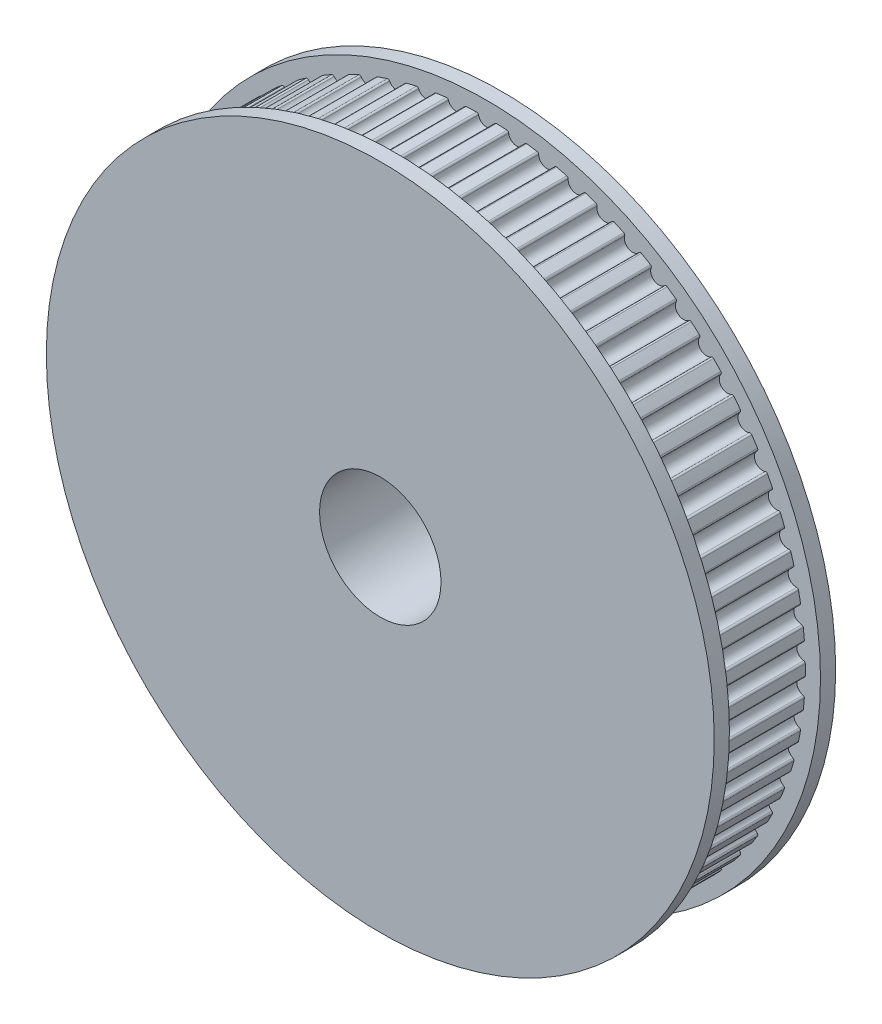
SolidWorks part; units mm, degrees
material "Plain Carbon Steel"
ref_plane "Front Plane" through (0, 0, 0) normal (0, 0, 1) x (1, 0, 0)
ref_plane "Top Plane" through (0, 0, 0) normal (0, 1, 0) x (1, 0, 0)
ref_plane "Right Plane" through (0, 0, 0) normal (1, 0, 0) x (0, 0, -1)
sketch "Sketch1" plane through (0, 0, 0) normal (0, 0, 1) x (1, 0, 0)
  circle A0 centre (0, 0) radius 4
  arc A1 (-0.655, 20.9898) -> (0.655, 20.9898) centre (0, 0) ccw
  arc A2 (-0.5287, 20.8902) -> (0.5287, 20.8902) centre (0, 21) ccw
  arc A3 (0.5287, 20.8902) -> (0.655, 20.9898) centre (0.6511, 20.8648) cw
  arc A4 (-0.5287, 20.8902) -> (-0.655, 20.9898) centre (-0.6511, 20.8648) ccw
  arc A5 (1.3432, 20.957) -> (2.6473, 20.8325) centre (0, 0) ccw
  arc A6 (1.4594, 20.8459) -> (1.3432, 20.957) centre (1.3352, 20.8323) ccw
  arc A7 (1.4594, 20.8459) -> (2.5121, 20.7454) centre (1.9962, 20.9049) ccw
  arc A8 (2.5121, 20.7454) -> (2.6473, 20.8325) centre (2.6315, 20.7085) cw
  arc A9 (3.3292, 20.7344) -> (4.6155, 20.4865) centre (0, 0) ccw
  arc A10 (3.4343, 20.6128) -> (3.3292, 20.7344) centre (3.3093, 20.611) ccw
  arc A11 (3.4343, 20.6128) -> (4.4727, 20.4127) centre (3.9743, 20.6205) ccw
  arc A12 (4.4727, 20.4127) -> (4.6155, 20.4865) centre (4.5881, 20.3646) cw
  arc A13 (5.285, 20.3241) -> (6.542, 19.955) centre (0, 0) ccw
  arc A14 (5.3782, 20.193) -> (5.285, 20.3241) centre (5.2536, 20.2031) ccw
  arc A15 (5.3782, 20.193) -> (6.3928, 19.8951) centre (5.9164, 20.1494) ccw
  arc A16 (6.3928, 19.8951) -> (6.542, 19.955) centre (6.5031, 19.8362) cw
  arc A17 (7.193, 19.7297) -> (8.4092, 19.2428) centre (0, 0) ccw
  arc A18 (7.2733, 19.5903) -> (7.193, 19.7297) centre (7.1502, 19.6122) ccw
  arc A19 (7.2733, 19.5903) -> (8.255, 19.1973) centre (7.8049, 19.4957) ccw
  arc A20 (8.255, 19.1973) -> (8.4092, 19.2428) centre (8.3592, 19.1283) cw
  arc A21 (9.0359, 18.9566) -> (10.2003, 18.3563) centre (0, 0) ccw
  arc A22 (9.1025, 18.8103) -> (9.0359, 18.9566) centre (8.9821, 18.8438) ccw
  arc A23 (9.1025, 18.8103) -> (10.0424, 18.3257) centre (9.6228, 18.6655) ccw
  arc A24 (10.0424, 18.3257) -> (10.2003, 18.3563) centre (10.1396, 18.2471) cw
  arc A25 (10.7969, 18.0119) -> (11.899, 17.3036) centre (0, 0) ccw
  arc A26 (10.8493, 17.8598) -> (10.7969, 18.0119) centre (10.7326, 17.9046) ccw
  arc A27 (10.8493, 17.8598) -> (11.7389, 17.2881) centre (11.3535, 17.6663) ccw
  arc A28 (11.7389, 17.2881) -> (11.899, 17.3036) centre (11.8281, 17.2006) cw
  arc A29 (12.4601, 16.904) -> (13.4899, 16.0942) centre (0, 0) ccw
  arc A30 (12.4979, 16.7477) -> (12.4601, 16.904) centre (12.386, 16.8034) ccw
  arc A31 (12.4979, 16.7477) -> (13.3291, 16.094) centre (12.9813, 16.5071) ccw
  arc A32 (13.3291, 16.094) -> (13.4899, 16.0942) centre (13.4096, 15.9984) cw
  arc A33 (14.0105, 15.643) -> (14.9587, 14.739) centre (0, 0) ccw
  arc A34 (14.0333, 15.4838) -> (14.0105, 15.643) centre (13.9272, 15.5499) ccw
  arc A35 (14.0333, 15.4838) -> (14.7986, 14.7541) centre (14.4917, 15.1984) ccw
  arc A36 (14.7986, 14.7541) -> (14.9587, 14.739) centre (14.8696, 14.6513) cw
  arc A37 (15.4341, 14.2404) -> (16.292, 13.2504) centre (0, 0) ccw
  arc A38 (15.4416, 14.0798) -> (15.4341, 14.2404) centre (15.3422, 14.1557) ccw
  arc A39 (15.4416, 14.0798) -> (16.134, 13.2806) centre (15.8707, 13.7521) ccw
  arc A40 (16.134, 13.2806) -> (16.292, 13.2504) centre (16.195, 13.1715) cw
  arc A41 (16.7178, 12.7088) -> (17.4777, 11.6417) centre (0, 0) ccw
  arc A42 (16.71, 12.5482) -> (16.7178, 12.7088) centre (16.6183, 12.6332) ccw
  arc A43 (16.71, 12.5482) -> (17.3234, 11.6868) centre (17.1061, 12.1812) ccw
  arc A44 (17.3234, 11.6868) -> (17.4777, 11.6417) centre (17.3737, 11.5724) cw
  arc A45 (17.8502, 11.0622) -> (18.5052, 9.9276) centre (0, 0) ccw
  arc A46 (17.8271, 10.903) -> (17.8502, 11.0622) centre (17.7439, 10.9963) ccw
  arc A47 (17.8271, 10.903) -> (18.3559, 9.9872) centre (18.1865, 10.5) ccw
  arc A48 (18.3559, 9.9872) -> (18.5052, 9.9276) centre (18.395, 9.8685) cw
  arc A49 (18.8209, 9.3153) -> (19.3651, 8.1236) centre (0, 0) ccw
  arc A50 (18.7828, 9.1591) -> (18.8209, 9.3153) centre (18.7088, 9.2598) ccw
  arc A51 (18.7828, 9.1591) -> (19.2221, 8.1972) centre (19.1023, 8.7237) ccw
  arc A52 (19.2221, 8.1972) -> (19.3651, 8.1236) centre (19.2498, 8.0753) cw
  arc A53 (19.6211, 7.4841) -> (20.0496, 6.2461) centre (0, 0) ccw
  arc A54 (19.5684, 7.3322) -> (19.6211, 7.4841) centre (19.5043, 7.4395) ccw
  arc A55 (19.5684, 7.3322) -> (19.9142, 6.3329) centre (19.845, 6.8684) ccw
  arc A56 (19.9142, 6.3329) -> (20.0496, 6.2461) centre (19.9303, 6.2089) cw
  arc A57 (20.2437, 5.5851) -> (20.5525, 4.312) centre (0, 0) ccw
  arc A58 (20.1767, 5.4389) -> (20.2437, 5.5851) centre (20.1232, 5.5518) ccw
  arc A59 (20.1767, 5.4389) -> (20.426, 4.4112) centre (20.408, 4.9509) ccw
  arc A60 (20.426, 4.4112) -> (20.5525, 4.312) centre (20.4302, 4.2863) cw
  arc A61 (20.6829, 3.6355) -> (20.8694, 2.3388) centre (0, 0) ccw
  arc A62 (20.6024, 3.4963) -> (20.6829, 3.6355) centre (20.5598, 3.6139) ccw
  arc A63 (20.6024, 3.4963) -> (20.7529, 2.4496) centre (20.7863, 2.9886) ccw
  arc A64 (20.7529, 2.4496) -> (20.8694, 2.3388) centre (20.7451, 2.3249) cw
  arc A65 (20.9348, 1.653) -> (20.9972, 0.3445) centre (0, 0) ccw
  arc A66 (20.8414, 1.5221) -> (20.9348, 1.653) centre (20.8102, 1.6432) ccw
  arc A67 (20.8414, 1.5221) -> (20.8917, 0.4659) centre (20.9762, 0.9992) ccw
  arc A68 (20.8917, 0.4659) -> (20.9972, 0.3445) centre (20.8722, 0.3424) cw
  arc A69 (20.9972, -0.3445) -> (20.9348, -1.653) centre (0, 0) ccw
  arc A70 (20.8917, -0.4659) -> (20.9972, -0.3445) centre (20.8722, -0.3424) ccw
  arc A71 (20.8917, -0.4659) -> (20.8414, -1.5221) centre (20.9762, -0.9992) ccw
  arc A72 (20.8414, -1.5221) -> (20.9348, -1.653) centre (20.8102, -1.6432) cw
  arc A73 (20.8694, -2.3388) -> (20.6829, -3.6355) centre (0, 0) ccw
  arc A74 (20.7529, -2.4496) -> (20.8694, -2.3388) centre (20.7451, -2.3249) ccw
  arc A75 (20.7529, -2.4496) -> (20.6024, -3.4963) centre (20.7863, -2.9886) ccw
  arc A76 (20.6024, -3.4963) -> (20.6829, -3.6355) centre (20.5598, -3.6139) cw
  arc A77 (20.5525, -4.312) -> (20.2437, -5.5851) centre (0, 0) ccw
  arc A78 (20.426, -4.4112) -> (20.5525, -4.312) centre (20.4302, -4.2863) ccw
  arc A79 (20.426, -4.4112) -> (20.1767, -5.4389) centre (20.408, -4.9509) ccw
  arc A80 (20.1767, -5.4389) -> (20.2437, -5.5851) centre (20.1232, -5.5518) cw
  arc A81 (20.0496, -6.2461) -> (19.6211, -7.4841) centre (0, 0) ccw
  arc A82 (19.9142, -6.3329) -> (20.0496, -6.2461) centre (19.9303, -6.2089) ccw
  arc A83 (19.9142, -6.3329) -> (19.5684, -7.3322) centre (19.845, -6.8684) ccw
  arc A84 (19.5684, -7.3322) -> (19.6211, -7.4841) centre (19.5043, -7.4395) cw
  arc A85 (19.3651, -8.1236) -> (18.8209, -9.3153) centre (0, 0) ccw
  arc A86 (19.2221, -8.1972) -> (19.3651, -8.1236) centre (19.2498, -8.0753) ccw
  arc A87 (19.2221, -8.1972) -> (18.7828, -9.1591) centre (19.1023, -8.7237) ccw
  arc A88 (18.7828, -9.1591) -> (18.8209, -9.3153) centre (18.7088, -9.2598) cw
  arc A89 (18.5052, -9.9276) -> (17.8502, -11.0622) centre (0, 0) ccw
  arc A90 (18.3559, -9.9872) -> (18.5052, -9.9276) centre (18.395, -9.8685) ccw
  arc A91 (18.3559, -9.9872) -> (17.8271, -10.903) centre (18.1865, -10.5) ccw
  arc A92 (17.8271, -10.903) -> (17.8502, -11.0622) centre (17.7439, -10.9963) cw
  arc A93 (17.4777, -11.6417) -> (16.7178, -12.7088) centre (0, 0) ccw
  arc A94 (17.3234, -11.6868) -> (17.4777, -11.6417) centre (17.3737, -11.5724) ccw
  arc A95 (17.3234, -11.6868) -> (16.71, -12.5482) centre (17.1061, -12.1812) ccw
  arc A96 (16.71, -12.5482) -> (16.7178, -12.7088) centre (16.6183, -12.6332) cw
  arc A97 (16.292, -13.2504) -> (15.4341, -14.2404) centre (0, 0) ccw
  arc A98 (16.134, -13.2806) -> (16.292, -13.2504) centre (16.195, -13.1715) ccw
  arc A99 (16.134, -13.2806) -> (15.4416, -14.0798) centre (15.8707, -13.7521) ccw
  arc A100 (15.4416, -14.0798) -> (15.4341, -14.2404) centre (15.3422, -14.1557) cw
  arc A101 (14.9587, -14.739) -> (14.0105, -15.643) centre (0, 0) ccw
  arc A102 (14.7986, -14.7541) -> (14.9587, -14.739) centre (14.8696, -14.6513) ccw
  arc A103 (14.7986, -14.7541) -> (14.0333, -15.4838) centre (14.4917, -15.1984) ccw
  arc A104 (14.0333, -15.4838) -> (14.0105, -15.643) centre (13.9272, -15.5499) cw
  arc A105 (13.4899, -16.0942) -> (12.4601, -16.904) centre (0, 0) ccw
  arc A106 (13.3291, -16.094) -> (13.4899, -16.0942) centre (13.4096, -15.9984) ccw
  arc A107 (13.3291, -16.094) -> (12.4979, -16.7477) centre (12.9813, -16.5071) ccw
  arc A108 (12.4979, -16.7477) -> (12.4601, -16.904) centre (12.386, -16.8034) cw
  arc A109 (11.899, -17.3036) -> (10.7969, -18.0119) centre (0, 0) ccw
  arc A110 (11.7389, -17.2881) -> (11.899, -17.3036) centre (11.8281, -17.2006) ccw
  arc A111 (11.7389, -17.2881) -> (10.8493, -17.8598) centre (11.3535, -17.6663) ccw
  arc A112 (10.8493, -17.8598) -> (10.7969, -18.0119) centre (10.7326, -17.9046) cw
  arc A113 (10.2003, -18.3563) -> (9.0359, -18.9566) centre (0, 0) ccw
  arc A114 (10.0424, -18.3257) -> (10.2003, -18.3563) centre (10.1396, -18.2471) ccw
  arc A115 (10.0424, -18.3257) -> (9.1025, -18.8103) centre (9.6228, -18.6655) ccw
  arc A116 (9.1025, -18.8103) -> (9.0359, -18.9566) centre (8.9821, -18.8438) cw
  arc A117 (8.4092, -19.2428) -> (7.193, -19.7297) centre (0, 0) ccw
  arc A118 (8.255, -19.1973) -> (8.4092, -19.2428) centre (8.3592, -19.1283) ccw
  arc A119 (8.255, -19.1973) -> (7.2733, -19.5903) centre (7.8049, -19.4957) ccw
  arc A120 (7.2733, -19.5903) -> (7.193, -19.7297) centre (7.1502, -19.6122) cw
  arc A121 (6.542, -19.955) -> (5.285, -20.3241) centre (0, 0) ccw
  arc A122 (6.3928, -19.8951) -> (6.542, -19.955) centre (6.5031, -19.8362) ccw
  arc A123 (6.3928, -19.8951) -> (5.3782, -20.193) centre (5.9164, -20.1494) ccw
  arc A124 (5.3782, -20.193) -> (5.285, -20.3241) centre (5.2536, -20.2031) cw
  arc A125 (4.6155, -20.4865) -> (3.3292, -20.7344) centre (0, 0) ccw
  arc A126 (4.4727, -20.4127) -> (4.6155, -20.4865) centre (4.5881, -20.3646) ccw
  arc A127 (4.4727, -20.4127) -> (3.4343, -20.6128) centre (3.9743, -20.6205) ccw
  arc A128 (3.4343, -20.6128) -> (3.3292, -20.7344) centre (3.3093, -20.611) cw
  arc A129 (2.6473, -20.8325) -> (1.3432, -20.957) centre (0, 0) ccw
  arc A130 (2.5121, -20.7454) -> (2.6473, -20.8325) centre (2.6315, -20.7085) ccw
  arc A131 (2.5121, -20.7454) -> (1.4594, -20.8459) centre (1.9962, -20.9049) ccw
  arc A132 (1.4594, -20.8459) -> (1.3432, -20.957) centre (1.3352, -20.8323) cw
  arc A133 (0.655, -20.9898) -> (-0.655, -20.9898) centre (0, 0) ccw
  arc A134 (0.5287, -20.8902) -> (0.655, -20.9898) centre (0.6511, -20.8648) ccw
  arc A135 (0.5287, -20.8902) -> (-0.5287, -20.8902) centre (0, -21) ccw
  arc A136 (-0.5287, -20.8902) -> (-0.655, -20.9898) centre (-0.6511, -20.8648) cw
  arc A137 (-1.3432, -20.957) -> (-2.6473, -20.8325) centre (0, 0) ccw
  arc A138 (-1.4594, -20.8459) -> (-1.3432, -20.957) centre (-1.3352, -20.8323) ccw
  arc A139 (-1.4594, -20.8459) -> (-2.5121, -20.7454) centre (-1.9962, -20.9049) ccw
  arc A140 (-2.5121, -20.7454) -> (-2.6473, -20.8325) centre (-2.6315, -20.7085) cw
  arc A141 (-3.3292, -20.7344) -> (-4.6155, -20.4865) centre (0, 0) ccw
  arc A142 (-3.4343, -20.6128) -> (-3.3292, -20.7344) centre (-3.3093, -20.611) ccw
  arc A143 (-3.4343, -20.6128) -> (-4.4727, -20.4127) centre (-3.9743, -20.6205) ccw
  arc A144 (-4.4727, -20.4127) -> (-4.6155, -20.4865) centre (-4.5881, -20.3646) cw
  arc A145 (-5.285, -20.3241) -> (-6.542, -19.955) centre (0, 0) ccw
  arc A146 (-5.3782, -20.193) -> (-5.285, -20.3241) centre (-5.2536, -20.2031) ccw
  arc A147 (-5.3782, -20.193) -> (-6.3928, -19.8951) centre (-5.9164, -20.1494) ccw
  arc A148 (-6.3928, -19.8951) -> (-6.542, -19.955) centre (-6.5031, -19.8362) cw
  arc A149 (-7.193, -19.7297) -> (-8.4092, -19.2428) centre (0, 0) ccw
  arc A150 (-7.2733, -19.5903) -> (-7.193, -19.7297) centre (-7.1502, -19.6122) ccw
  arc A151 (-7.2733, -19.5903) -> (-8.255, -19.1973) centre (-7.8049, -19.4957) ccw
  arc A152 (-8.255, -19.1973) -> (-8.4092, -19.2428) centre (-8.3592, -19.1283) cw
  arc A153 (-9.0359, -18.9566) -> (-10.2003, -18.3563) centre (0, 0) ccw
  arc A154 (-9.1025, -18.8103) -> (-9.0359, -18.9566) centre (-8.9821, -18.8438) ccw
  arc A155 (-9.1025, -18.8103) -> (-10.0424, -18.3257) centre (-9.6228, -18.6655) ccw
  arc A156 (-10.0424, -18.3257) -> (-10.2003, -18.3563) centre (-10.1396, -18.2471) cw
  arc A157 (-10.7969, -18.0119) -> (-11.899, -17.3036) centre (0, 0) ccw
  arc A158 (-10.8493, -17.8598) -> (-10.7969, -18.0119) centre (-10.7326, -17.9046) ccw
  arc A159 (-10.8493, -17.8598) -> (-11.7389, -17.2881) centre (-11.3535, -17.6663) ccw
  arc A160 (-11.7389, -17.2881) -> (-11.899, -17.3036) centre (-11.8281, -17.2006) cw
  arc A161 (-12.4601, -16.904) -> (-13.4899, -16.0942) centre (0, 0) ccw
  arc A162 (-12.4979, -16.7477) -> (-12.4601, -16.904) centre (-12.386, -16.8034) ccw
  arc A163 (-12.4979, -16.7477) -> (-13.3291, -16.094) centre (-12.9813, -16.5071) ccw
  arc A164 (-13.3291, -16.094) -> (-13.4899, -16.0942) centre (-13.4096, -15.9984) cw
  arc A165 (-14.0105, -15.643) -> (-14.9587, -14.739) centre (0, 0) ccw
  arc A166 (-14.0333, -15.4838) -> (-14.0105, -15.643) centre (-13.9272, -15.5499) ccw
  arc A167 (-14.0333, -15.4838) -> (-14.7986, -14.7541) centre (-14.4917, -15.1984) ccw
  arc A168 (-14.7986, -14.7541) -> (-14.9587, -14.739) centre (-14.8696, -14.6513) cw
  arc A169 (-15.4341, -14.2404) -> (-16.292, -13.2504) centre (0, 0) ccw
  arc A170 (-15.4416, -14.0798) -> (-15.4341, -14.2404) centre (-15.3422, -14.1557) ccw
  arc A171 (-15.4416, -14.0798) -> (-16.134, -13.2806) centre (-15.8707, -13.7521) ccw
  arc A172 (-16.134, -13.2806) -> (-16.292, -13.2504) centre (-16.195, -13.1715) cw
  arc A173 (-16.7178, -12.7088) -> (-17.4777, -11.6417) centre (0, 0) ccw
  arc A174 (-16.71, -12.5482) -> (-16.7178, -12.7088) centre (-16.6183, -12.6332) ccw
  arc A175 (-16.71, -12.5482) -> (-17.3234, -11.6868) centre (-17.1061, -12.1812) ccw
  arc A176 (-17.3234, -11.6868) -> (-17.4777, -11.6417) centre (-17.3737, -11.5724) cw
  arc A177 (-17.8502, -11.0622) -> (-18.5052, -9.9276) centre (0, 0) ccw
  arc A178 (-17.8271, -10.903) -> (-17.8502, -11.0622) centre (-17.7439, -10.9963) ccw
  arc A179 (-17.8271, -10.903) -> (-18.3559, -9.9872) centre (-18.1865, -10.5) ccw
  arc A180 (-18.3559, -9.9872) -> (-18.5052, -9.9276) centre (-18.395, -9.8685) cw
  arc A181 (-18.8209, -9.3153) -> (-19.3651, -8.1236) centre (0, 0) ccw
  arc A182 (-18.7828, -9.1591) -> (-18.8209, -9.3153) centre (-18.7088, -9.2598) ccw
  arc A183 (-18.7828, -9.1591) -> (-19.2221, -8.1972) centre (-19.1023, -8.7237) ccw
  arc A184 (-19.2221, -8.1972) -> (-19.3651, -8.1236) centre (-19.2498, -8.0753) cw
  arc A185 (-19.6211, -7.4841) -> (-20.0496, -6.2461) centre (0, 0) ccw
  arc A186 (-19.5684, -7.3322) -> (-19.6211, -7.4841) centre (-19.5043, -7.4395) ccw
  arc A187 (-19.5684, -7.3322) -> (-19.9142, -6.3329) centre (-19.845, -6.8684) ccw
  arc A188 (-19.9142, -6.3329) -> (-20.0496, -6.2461) centre (-19.9303, -6.2089) cw
  arc A189 (-20.2437, -5.5851) -> (-20.5525, -4.312) centre (0, 0) ccw
  arc A190 (-20.1767, -5.4389) -> (-20.2437, -5.5851) centre (-20.1232, -5.5518) ccw
  arc A191 (-20.1767, -5.4389) -> (-20.426, -4.4112) centre (-20.408, -4.9509) ccw
  arc A192 (-20.426, -4.4112) -> (-20.5525, -4.312) centre (-20.4302, -4.2863) cw
  arc A193 (-20.6829, -3.6355) -> (-20.8694, -2.3388) centre (0, 0) ccw
  arc A194 (-20.6024, -3.4963) -> (-20.6829, -3.6355) centre (-20.5598, -3.6139) ccw
  arc A195 (-20.6024, -3.4963) -> (-20.7529, -2.4496) centre (-20.7863, -2.9886) ccw
  arc A196 (-20.7529, -2.4496) -> (-20.8694, -2.3388) centre (-20.7451, -2.3249) cw
  arc A197 (-20.9348, -1.653) -> (-20.9972, -0.3445) centre (0, 0) ccw
  arc A198 (-20.8414, -1.5221) -> (-20.9348, -1.653) centre (-20.8102, -1.6432) ccw
  arc A199 (-20.8414, -1.5221) -> (-20.8917, -0.4659) centre (-20.9762, -0.9992) ccw
  arc A200 (-20.8917, -0.4659) -> (-20.9972, -0.3445) centre (-20.8722, -0.3424) cw
  arc A201 (-20.9972, 0.3445) -> (-20.9348, 1.653) centre (0, 0) ccw
  arc A202 (-20.8917, 0.4659) -> (-20.9972, 0.3445) centre (-20.8722, 0.3424) ccw
  arc A203 (-20.8917, 0.4659) -> (-20.8414, 1.5221) centre (-20.9762, 0.9992) ccw
  arc A204 (-20.8414, 1.5221) -> (-20.9348, 1.653) centre (-20.8102, 1.6432) cw
  arc A205 (-20.8694, 2.3388) -> (-20.6829, 3.6355) centre (0, 0) ccw
  arc A206 (-20.7529, 2.4496) -> (-20.8694, 2.3388) centre (-20.7451, 2.3249) ccw
  arc A207 (-20.7529, 2.4496) -> (-20.6024, 3.4963) centre (-20.7863, 2.9886) ccw
  arc A208 (-20.6024, 3.4963) -> (-20.6829, 3.6355) centre (-20.5598, 3.6139) cw
  arc A209 (-20.5525, 4.312) -> (-20.2437, 5.5851) centre (0, 0) ccw
  arc A210 (-20.426, 4.4112) -> (-20.5525, 4.312) centre (-20.4302, 4.2863) ccw
  arc A211 (-20.426, 4.4112) -> (-20.1767, 5.4389) centre (-20.408, 4.9509) ccw
  arc A212 (-20.1767, 5.4389) -> (-20.2437, 5.5851) centre (-20.1232, 5.5518) cw
  arc A213 (-20.0496, 6.2461) -> (-19.6211, 7.4841) centre (0, 0) ccw
  arc A214 (-19.9142, 6.3329) -> (-20.0496, 6.2461) centre (-19.9303, 6.2089) ccw
  arc A215 (-19.9142, 6.3329) -> (-19.5684, 7.3322) centre (-19.845, 6.8684) ccw
  arc A216 (-19.5684, 7.3322) -> (-19.6211, 7.4841) centre (-19.5043, 7.4395) cw
  arc A217 (-19.3651, 8.1236) -> (-18.8209, 9.3153) centre (0, 0) ccw
  arc A218 (-19.2221, 8.1972) -> (-19.3651, 8.1236) centre (-19.2498, 8.0753) ccw
  arc A219 (-19.2221, 8.1972) -> (-18.7828, 9.1591) centre (-19.1023, 8.7237) ccw
  arc A220 (-18.7828, 9.1591) -> (-18.8209, 9.3153) centre (-18.7088, 9.2598) cw
  arc A221 (-18.5052, 9.9276) -> (-17.8502, 11.0622) centre (0, 0) ccw
  arc A222 (-18.3559, 9.9872) -> (-18.5052, 9.9276) centre (-18.395, 9.8685) ccw
  arc A223 (-18.3559, 9.9872) -> (-17.8271, 10.903) centre (-18.1865, 10.5) ccw
  arc A224 (-17.8271, 10.903) -> (-17.8502, 11.0622) centre (-17.7439, 10.9963) cw
  arc A225 (-17.4777, 11.6417) -> (-16.7178, 12.7088) centre (0, 0) ccw
  arc A226 (-17.3234, 11.6868) -> (-17.4777, 11.6417) centre (-17.3737, 11.5724) ccw
  arc A227 (-17.3234, 11.6868) -> (-16.71, 12.5482) centre (-17.1061, 12.1812) ccw
  arc A228 (-16.71, 12.5482) -> (-16.7178, 12.7088) centre (-16.6183, 12.6332) cw
  arc A229 (-16.292, 13.2504) -> (-15.4341, 14.2404) centre (0, 0) ccw
  arc A230 (-16.134, 13.2806) -> (-16.292, 13.2504) centre (-16.195, 13.1715) ccw
  arc A231 (-16.134, 13.2806) -> (-15.4416, 14.0798) centre (-15.8707, 13.7521) ccw
  arc A232 (-15.4416, 14.0798) -> (-15.4341, 14.2404) centre (-15.3422, 14.1557) cw
  arc A233 (-14.9587, 14.739) -> (-14.0105, 15.643) centre (0, 0) ccw
  arc A234 (-14.7986, 14.7541) -> (-14.9587, 14.739) centre (-14.8696, 14.6513) ccw
  arc A235 (-14.7986, 14.7541) -> (-14.0333, 15.4838) centre (-14.4917, 15.1984) ccw
  arc A236 (-14.0333, 15.4838) -> (-14.0105, 15.643) centre (-13.9272, 15.5499) cw
  arc A237 (-13.4899, 16.0942) -> (-12.4601, 16.904) centre (0, 0) ccw
  arc A238 (-13.3291, 16.094) -> (-13.4899, 16.0942) centre (-13.4096, 15.9984) ccw
  arc A239 (-13.3291, 16.094) -> (-12.4979, 16.7477) centre (-12.9813, 16.5071) ccw
  arc A240 (-12.4979, 16.7477) -> (-12.4601, 16.904) centre (-12.386, 16.8034) cw
  arc A241 (-11.899, 17.3036) -> (-10.7969, 18.0119) centre (0, 0) ccw
  arc A242 (-11.7389, 17.2881) -> (-11.899, 17.3036) centre (-11.8281, 17.2006) ccw
  arc A243 (-11.7389, 17.2881) -> (-10.8493, 17.8598) centre (-11.3535, 17.6663) ccw
  arc A244 (-10.8493, 17.8598) -> (-10.7969, 18.0119) centre (-10.7326, 17.9046) cw
  arc A245 (-10.2003, 18.3563) -> (-9.0359, 18.9566) centre (0, 0) ccw
  arc A246 (-10.0424, 18.3257) -> (-10.2003, 18.3563) centre (-10.1396, 18.2471) ccw
  arc A247 (-10.0424, 18.3257) -> (-9.1025, 18.8103) centre (-9.6228, 18.6655) ccw
  arc A248 (-9.1025, 18.8103) -> (-9.0359, 18.9566) centre (-8.9821, 18.8438) cw
  arc A249 (-8.4092, 19.2428) -> (-7.193, 19.7297) centre (0, 0) ccw
  arc A250 (-8.255, 19.1973) -> (-8.4092, 19.2428) centre (-8.3592, 19.1283) ccw
  arc A251 (-8.255, 19.1973) -> (-7.2733, 19.5903) centre (-7.8049, 19.4957) ccw
  arc A252 (-7.2733, 19.5903) -> (-7.193, 19.7297) centre (-7.1502, 19.6122) cw
  arc A253 (-6.542, 19.955) -> (-5.285, 20.3241) centre (0, 0) ccw
  arc A254 (-6.3928, 19.8951) -> (-6.542, 19.955) centre (-6.5031, 19.8362) ccw
  arc A255 (-6.3928, 19.8951) -> (-5.3782, 20.193) centre (-5.9164, 20.1494) ccw
  arc A256 (-5.3782, 20.193) -> (-5.285, 20.3241) centre (-5.2536, 20.2031) cw
  arc A257 (-4.6155, 20.4865) -> (-3.3292, 20.7344) centre (0, 0) ccw
  arc A258 (-4.4727, 20.4127) -> (-4.6155, 20.4865) centre (-4.5881, 20.3646) ccw
  arc A259 (-4.4727, 20.4127) -> (-3.4343, 20.6128) centre (-3.9743, 20.6205) ccw
  arc A260 (-3.4343, 20.6128) -> (-3.3292, 20.7344) centre (-3.3093, 20.611) cw
  arc A261 (-2.6473, 20.8325) -> (-1.3432, 20.957) centre (0, 0) ccw
  arc A262 (-2.5121, 20.7454) -> (-2.6473, 20.8325) centre (-2.6315, 20.7085) ccw
  arc A263 (-2.5121, 20.7454) -> (-1.4594, 20.8459) centre (-1.9962, 20.9049) ccw
  arc A264 (-1.4594, 20.8459) -> (-1.3432, 20.957) centre (-1.3352, 20.8323) cw
  point P469 (0, 0)
  dimension "D1" = 0.125
extrude "Boss-Extrude1" add sketch "Sketch1" along normal blind 6
sketch "Sketch2" plane through (0, 0, 6) normal (0, 0, 1) x (1, 0, 0)
  circle A0 centre (0, 0) radius 4
  circle A1 centre (0, 0) radius 22
extrude "Boss-Extrude2" add sketch "Sketch2" along normal blind 1
sketch "Sketch3" plane through (0, 0, 0) normal (0, 0, -1) x (-1, 0, 0)
  circle A0 centre (0, 0) radius 4
  circle A1 centre (0, 0) radius 22
extrude "Boss-Extrude3" add sketch "Sketch3" along normal blind 1
